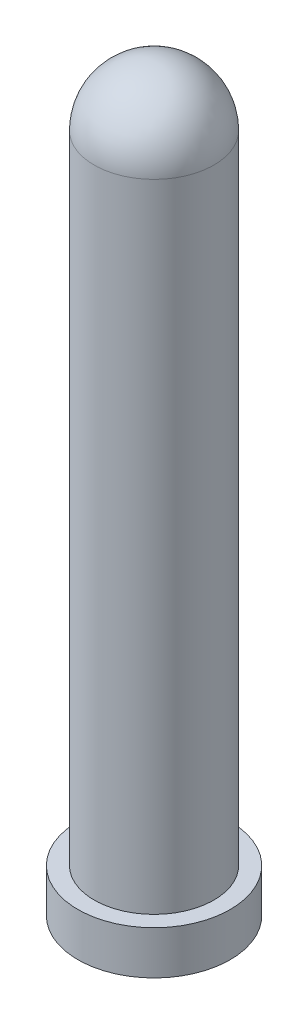
SolidWorks part; units mm, degrees
ref_plane "Plan de face" through (0, 0, 0) normal (0, 0, 1) x (1, 0, 0)
ref_plane "Plan de dessus" through (0, 0, 0) normal (0, 1, 0) x (1, 0, 0)
ref_plane "Plan de droite" through (0, 0, 0) normal (1, 0, 0) x (0, 0, -1)
sketch "Esquisse1" plane through (0, 0, 0) normal (0, 0, 1) x (1, 0, 0)
  line L0 (0, 0) -> (0, 44.3604) construction
  line L1 (-1.5, 0) -> (-1.5, 30)
  line L2 (-1.5, 0) -> (-3.5, 0)
  line L3 (-3.5, 0) -> (-3.5, 2)
  line L4 (-3.5, 2) -> (-2.75, 2)
  line L5 (-2.75, 2) -> (-2.75, 31.25)
  line L6 (-1.5, 30) -> (0, 30)
  line L7 (0, 30) -> (0, 34)
  arc A1 (0, 34) -> (-2.75, 31.25) centre (0, 31.25) ccw
  dimension "D1" = 3
  dimension "D2" = 5.5
  dimension "D3" = 2
  dimension "D4" = 7
  dimension "D5" = 34
  dimension "D6" = 30
revolve "Révolution1" add sketch "Esquisse1" angle 360 about L0
